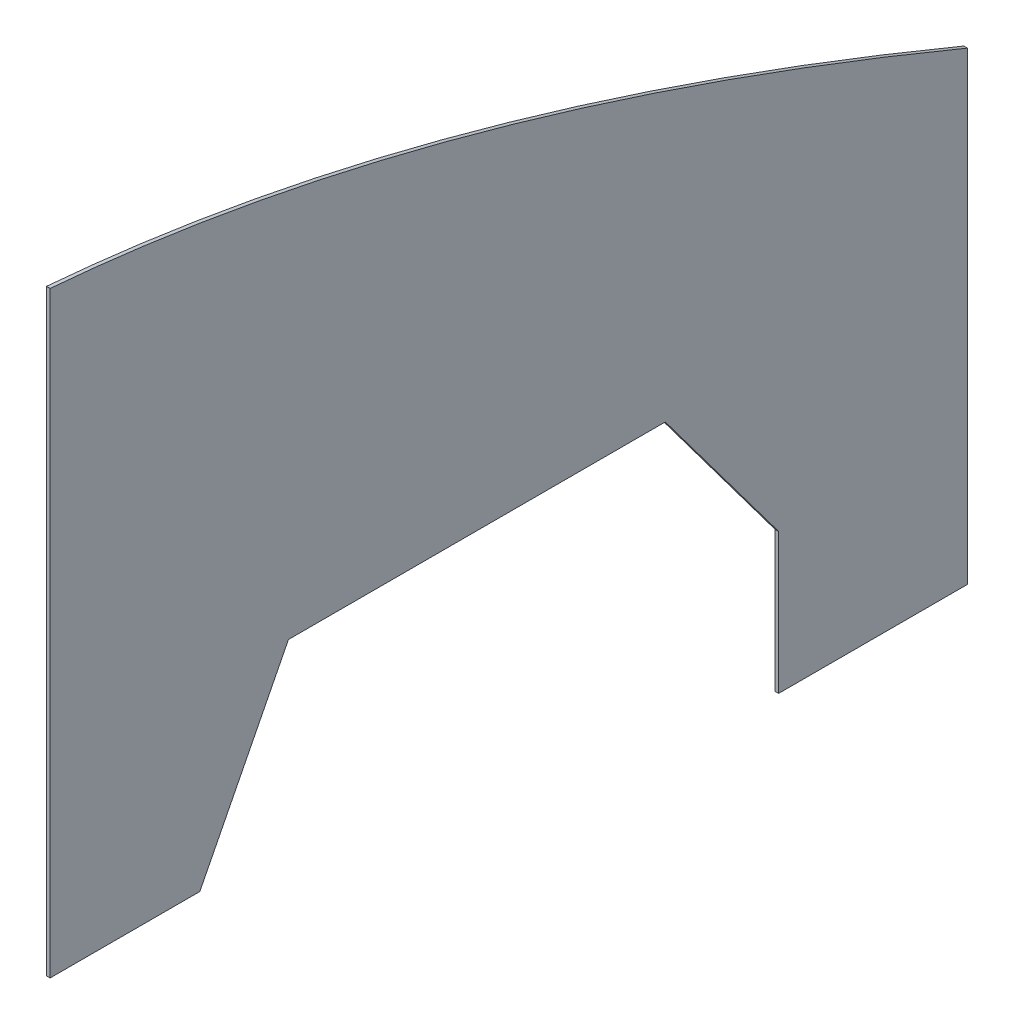
SolidWorks part; units mm, degrees
ref_plane "Front" through (0, 0, 0) normal (0, 0, 1) x (1, 0, 0)
ref_plane "Top" through (0, 0, 0) normal (0, 1, 0) x (1, 0, 0)
ref_plane "Right" through (0, 0, 0) normal (1, 0, 0) x (0, 0, -1)
sketch "Sketch1" plane through (0, 0, 0) normal (1, 0, 0) x (0, 0, -1)
  line L0 (0, 0) -> (0, 332)
  line L2 (510, 192.7) -> (510, 0)
  line L4 (510, 0) -> (510, -65.5)
  line L5 (510, -65.5) -> (405, -65.5)
  line L6 (405, -65.5) -> (405, 12.5)
  line L11 (132.5, 96.7) -> (342, 96.7)
  line L12 (342, 96.7) -> (405, 12.5)
  line L13 (132.5, 96.7) -> (83.2462, 0)
  line L14 (83.2462, 0) -> (0, 0)
  spline S0 degree 2 poles (0, 332) (217.96, 314.0311) (510, 192.7) knots 0 0 0 1 1 1
  dimension "D1" = 332
  dimension "D2" = 510
  dimension "D3" = 192.7
  dimension "D4" = 65.5
  dimension "D5" = 105
  dimension "D6" = 78
  dimension "D7" = 209.5
  dimension "D8" = 168
  dimension "D9" = 96.7
extrude "Boss-Extrude1" add sketch "Sketch1" along normal blind 2
